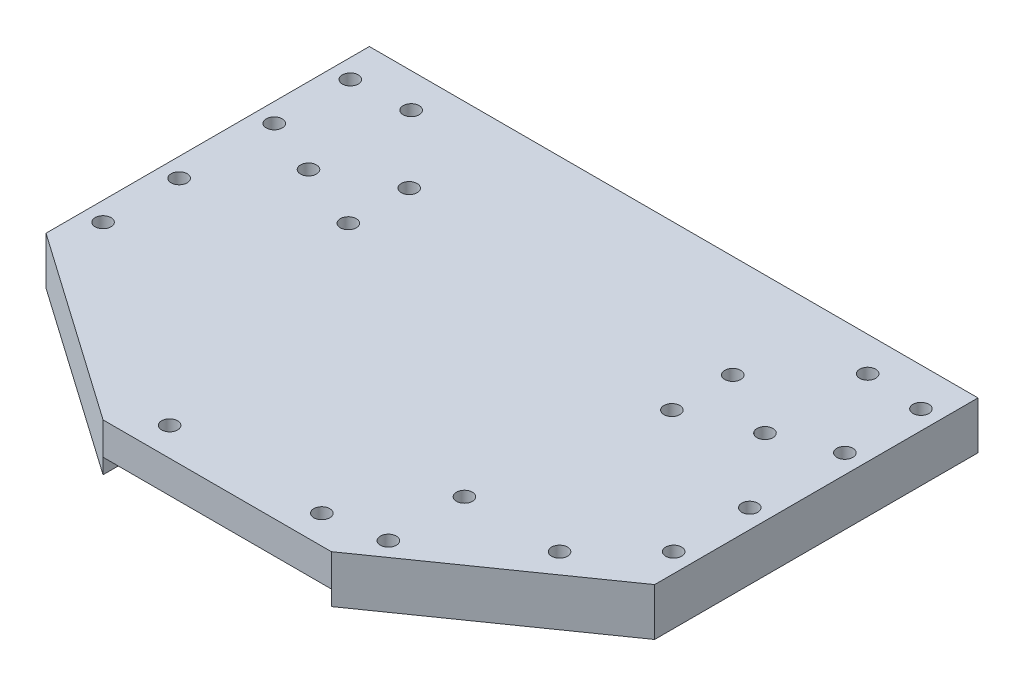
SolidWorks part; units mm, degrees
ref_plane "Front Plane" through (0, 0, 0) normal (0, 0, 1) x (1, 0, 0)
ref_plane "Top Plane" through (0, 0, 0) normal (0, 1, 0) x (1, 0, 0)
ref_plane "Right Plane" through (0, 0, 0) normal (1, 0, 0) x (0, 0, -1)
sketch "Sketch1" plane through (0, 0, 0) normal (0, 1, 0) x (1, 0, 0)
  line L2 (-80, -42.5) -> (-80, 42.5)
  line L3 (-80, 42.5) -> (80, 42.5)
  line L4 (80, -42.5) -> (80, 42.5)
  line L9 (-80, -42.5) -> (-30, -77.5)
  line L12 (-30, -77.5) -> (30, -77.5)
  line L14 (30, -77.5) -> (80, -42.5)
  point P0 (0, 0)
  dimension "D1" = 85
  dimension "D2" = 160
  dimension "D3" = 60
extrude "Boss-Extrude2" add sketch "Sketch1" along normal blind 12.5
sketch "Sketch2" plane through (0, 12.5, 0) normal (0, 1, 0) x (1, 0, 0)
  line L0 (0, 42.5) -> (0, 2.75) construction
  line L1 (80, 42.5) -> (-80, 42.5) construction
  line L2 (-30, -77.5) -> (30, -77.5) construction
  line L3 (-15, -27.25) -> (15, -27.25) construction
  line L4 (-10.25, -47.5) -> (10.25, -47.5)
  line L5 (-10.25, -47.5) -> (-10.25, -7)
  line L6 (-10.25, -7) -> (-3, -7)
  line L7 (10.25, -47.5) -> (10.25, -7)
  line L8 (-10.25, -47.5) -> (10.25, -7) construction
  line L9 (-10.25, -7) -> (10.25, -47.5) construction
  line L10 (-15, -57.25) -> (15, -57.25)
  line L11 (-15, -57.25) -> (-15, 2.75)
  line L12 (-15, 2.75) -> (15, 2.75)
  line L13 (15, -57.25) -> (15, 2.75)
  line L14 (-15, -57.25) -> (15, 2.75) construction
  line L15 (-15, 2.75) -> (15, -57.25) construction
  line L16 (3, -7) -> (3, 2.75)
  line L19 (3, 2.75) -> (-3, 2.75)
  line L20 (-3, -7) -> (-3, 2.75)
  line L21 (0, -7) -> (0, -77.5) construction
  line L22 (3, -7) -> (10.25, -7)
  circle A0 centre (-5, -51.5) radius 2.1
  circle A1 centre (5, -51.5) radius 2.1
  circle A2 centre (5, -3) radius 2.1
  circle A3 centre (-5, -3) radius 2.1
  point P6 (0, -27.25)
  point P11 (0, -27.25)
  dimension "D6" = 5
  dimension "D7" = 4
  dimension "D8" = 4.2
  dimension "D1" = 20.5
  dimension "D2" = 40.5
  dimension "D3" = 30
  dimension "D4" = 60
  dimension "D5" = 30
  dimension "D9" = 3
extrude "Boss-Extrude3" add sketch "Sketch2" along normal blind 29 contours L20 A3 L12 L11 L10 L13 L16 A2 L22 L7 L4 L5 L6 A0 A1
sketch "Sketch4" plane through (0, 0, 57.25) normal (0, 0, 1) x (1, 0, 0)
  line L0 (-5, 41.5) -> (-5, 12.5) construction
  line L1 (-15, 41.5) -> (15, 41.5) construction
  line L2 (-15, 12.5) -> (15, 12.5) construction
  line L3 (0, 41.5) -> (0, 12.5) construction
  line L4 (5, 41.5) -> (5, 12.5) construction
  line L5 (9.5, 37.5) -> (0.5, 37.5)
  line L6 (-9.5, 34) -> (-0.5, 34)
  line L7 (-9.5, 34) -> (-9.5, 37.5)
  line L8 (-9.5, 37.5) -> (-0.5, 37.5)
  line L9 (-0.5, 34) -> (-0.5, 37.5)
  line L10 (-9.5, 34) -> (-0.5, 37.5) construction
  line L11 (-9.5, 37.5) -> (-0.5, 34) construction
  line L12 (0.5, 34) -> (0.5, 37.5)
  line L13 (9.5, 34) -> (0.5, 34)
  line L14 (9.5, 34) -> (9.5, 37.5)
  point P10 (-5, 35.75)
  dimension "D1" = 5
  dimension "D2" = 9
  dimension "D3" = 3.5
  dimension "D4" = 4
extrude "Cut-Extrude1" cut sketch "Sketch4" against normal blind 73
chamfer "Chamfer1" distance 3 angle 45 4 edges at (-15, 27, -2.75) (15, 27, -2.75) (-15, 27, 57.25) (15, 27, 57.25)
sketch "Sketch5" plane through (0, 0, 0) normal (0, -1, 0) x (1, 0, 0)
  line L0 (-30, 70) -> (30, 70) construction
  line L1 (-30, 77.5) -> (30, 77.5)
  line L2 (-30, 77.5) -> (-30, 62.5)
  line L3 (-30, 62.5) -> (30, 62.5)
  line L4 (30, 77.5) -> (30, 62.5)
  line L5 (0, 77.5) -> (0, 62.5) construction
  circle A0 centre (-20, 70) radius 2.8976
  circle A1 centre (20, 70) radius 2.8976
  point P11 (0, 70)
  dimension "D2" = 20
  dimension "D1" = 15
extrude "Cut-Extrude2" cut sketch "Sketch5" against normal blind 4
sketch "Sketch6" plane through (0, 0, 0) normal (0, -1, 0) x (-1, 0, 0)
  circle A0 centre (20, -70) radius 2.8976
  circle A1 centre (-20, -70) radius 2.8976
extrude "Cut-Extrude3" cut sketch "Sketch6" against normal blind 26
sketch "Sketch7" plane through (0, 12.5, 0) normal (0, 1, 0) x (1, 0, 0)
  line L0 (-75, 34.6) -> (-75, 30.4) construction
  line L5 (-75, 14.6) -> (-75, 10.4) construction
  line L6 (0, 42.5) -> (0, -77.5) construction
  line L7 (80, 42.5) -> (-80, 42.5) construction
  line L8 (-30, -77.5) -> (30, -77.5) construction
  line L10 (75, 34.6) -> (75, 30.4) construction
  line L15 (-75, -10.4) -> (-75, -14.6) construction
  line L16 (-75, -30.4) -> (-75, -34.6) construction
  line L17 (75, -10.4) -> (75, -14.6) construction
  line L18 (75, -30.4) -> (75, -34.6) construction
  line L19 (75, 14.6) -> (75, 10.4) construction
  circle A0 centre (-75, 32.5) radius 2.1
  circle A1 centre (-75, 12.5) radius 2.1
  circle A2 centre (-75, -12.5) radius 2.1
  circle A3 centre (-75, -32.5) radius 2.1
  circle A4 centre (75, -32.5) radius 2.1
  circle A5 centre (75, -12.5) radius 2.1
  circle A6 centre (75, 12.5) radius 2.1
  circle A7 centre (75, 32.5) radius 2.1
  dimension "D2" = 4.2
  dimension "D4" = 4.2
extrude "Cut-Extrude4" cut sketch "Sketch7" against normal blind 26
sketch "Sketch8" plane through (0, 0, 0) normal (0, -1, 0) x (1, 0, 0)
  line L0 (0, 77.5) -> (0, -42.5) construction
  line L5 (30, 77.5) -> (-30, 77.5) construction
  line L6 (80, -42.5) -> (-80, -42.5) construction
  line L7 (-60, 2.5) -> (-60, -8.6) construction
  line L8 (-70, -42.5) -> (-60, -42.5)
  line L12 (-60, -20) -> (-70, -20) construction
  line L13 (-60, -31.4) -> (-60, -42.5) construction
  circle A0 centre (-60, -6.5) radius 2.1
  circle A1 centre (-60, -33.5) radius 2.1
  circle A2 centre (60, -33.5) radius 2.1
  circle A3 centre (60, -6.5) radius 2.1
  dimension "D4" = 4.2
extrude "Cut-Extrude5" cut sketch "Sketch8" against normal blind 26 contours A0 | A1 | A3 | A2
sketch "Sketch9" plane through (0, 0, 0) normal (0, -1, 0) x (1, 0, 0)
  line L0 (-60, -33.5) -> (-60, -6.5) construction
  line L1 (80, -42.5) -> (-80, -42.5) construction
  line L2 (-70, -42.5) -> (-50, -42.5)
  line L3 (-70, -42.5) -> (-70, 2.5)
  line L4 (-70, 2.5) -> (-50, 2.5)
  line L5 (-50, -42.5) -> (-50, 2.5)
  line L6 (-80, -42.5) -> (-80, 42.5) construction
  line L7 (0, 77.5) -> (0, -43.6165) construction
  line L8 (30, 77.5) -> (-30, 77.5) construction
  line L9 (70, 2.5) -> (50, 2.5)
  line L10 (50, -42.5) -> (50, 2.5)
  line L11 (70, -42.5) -> (50, -42.5)
  line L12 (70, -42.5) -> (70, 2.5)
  dimension "D1" = 10
  dimension "D2" = 20
  dimension "D3" = 45
extrude "Cut-Extrude8" cut sketch "Sketch9" against normal blind 5
sketch "Sketch10" plane through (0, 0, 57.25) normal (0, 0, 1) x (1, 0, 0)
  line L0 (-0.5, 35.75) -> (0.5, 35.75) construction
  line L1 (-0.5, 34) -> (-0.5, 37.5) construction
  line L2 (0.5, 37.5) -> (0.5, 34) construction
  line L3 (9.5, 37.5) -> (0.5, 37.5) construction
  line L4 (-0.75, 34) -> (0.75, 34)
  line L5 (-0.75, 34) -> (-0.75, 37.5)
  line L6 (-0.75, 37.5) -> (0.75, 37.5)
  line L7 (0.75, 34) -> (0.75, 37.5)
  line L8 (-0.75, 34) -> (0.75, 37.5) construction
  line L9 (-0.75, 37.5) -> (0.75, 34) construction
  point P6 (0, 35.75)
  dimension "D1" = 1.5
extrude "Boss-Extrude4" add sketch "Sketch10" against normal up to surface (9.75 mm away) up to face at (-5, 35.75, 47.5)
sketch "Sketch11" plane through (0, 12.5, 0) normal (0, 1, 0) x (1, 0, 0)
  line L0 (0, -77.5) -> (0, 42.5) construction
  line L1 (-30, -77.5) -> (30, -77.5) construction
  line L2 (80, 42.5) -> (-80, 42.5) construction
  line L3 (-12, 2.75) -> (-3, 2.75) construction
  line L4 (0, 17.75) -> (-47.61, 17.75)
  line L5 (0, 17.75) -> (0, 42.75)
  line L6 (0, 42.75) -> (-47.61, 42.75)
  line L7 (-47.61, 17.75) -> (-47.61, 42.75)
  line L8 (-32.5, 42.75) -> (-32.5, 17.75) construction
  line L9 (-47.61, 30.25) -> (0, 30.25) construction
  circle A0 centre (-42.5, 37.25) radius 2.1
  circle A1 centre (-42.5, 23.25) radius 2.1
  dimension "D5" = 4.2
  dimension "D6" = 7
  dimension "D7" = 10
  dimension "D1" = 47.61
  dimension "D2" = 25
  dimension "D3" = 15
  dimension "D4" = 32.5
extrude "Cut-Extrude9" cut sketch "Sketch11" against normal blind 22 contours A0 | A1
sketch "Sketch12" plane through (0, 12.5, 0) normal (0, 1, 0) x (1, 0, 0)
  circle A0 centre (-42.5, 37.25) radius 2.1
  circle A1 centre (-42.5, 23.25) radius 2.1
extrude "Boss-Extrude5" add sketch "Sketch12" against normal through all
sketch "Sketch13" plane through (0, 41.5, 0) normal (0, 1, 0) x (1, 0, 0)
  line L1 (-18.0115, -62.004) -> (18.0115, -62.004)
  line L2 (-18.0115, -62.004) -> (-18.0115, 7.9434)
  line L3 (-18.0115, 7.9434) -> (18.0115, 7.9434)
  line L4 (18.0115, -62.004) -> (18.0115, 7.9434)
  line L5 (-18.0115, -62.004) -> (18.0115, 7.9434) construction
  line L6 (-18.0115, 7.9434) -> (18.0115, -62.004) construction
  point P0 (0, -27.0303)
extrude "Cut-Extrude10" cut sketch "Sketch13" against normal up to surface (29 mm away) up to face at (-5, 12.5, 53.6)
sketch "Sketch14" plane through (0, 12.5, 0) normal (0, 1, 0) x (1, 0, 0)
  circle A0 centre (-20, -70) radius 2.1
  circle A1 centre (20, -70) radius 2.1
  circle A2 centre (-20, -70) radius 2.8976
  circle A3 centre (20, -70) radius 2.8976
  dimension "D1" = 4.2
  dimension "D2" = 4.2
extrude "Boss-Extrude6" add sketch "Sketch14" against normal up to surface (8.5 mm away) up to face at (20, 4, 67.1024)
sketch "Sketch15" plane through (0, 12.5, 0) normal (0, 1, 0) x (1, 0, 0)
  line L0 (0, 42.5) -> (0, -77.5) construction
  line L1 (80, 42.5) -> (-80, 42.5) construction
  line L2 (-30, -77.5) -> (30, -77.5) construction
  line L3 (-47.53, 7.5) -> (0, 7.5) construction
  line L4 (0, 42.5) -> (-47.53, 42.5)
  line L5 (0, 42.5) -> (0, 22.5)
  line L6 (0, 22.5) -> (-47.53, 22.5)
  line L7 (-47.53, 42.5) -> (-47.53, 22.5)
  line L8 (0, 22.5) -> (-47.53, 22.5)
  line L9 (0, 22.5) -> (0, -7.5)
  line L10 (0, -7.5) -> (-47.53, -7.5)
  line L11 (-47.53, 22.5) -> (-47.53, -7.5)
  circle A0 centre (-42.53, 15.5) radius 2.1
  circle A1 centre (-42.53, -0.5) radius 2.1
  circle A2 centre (42.53, -0.5) radius 2.1
  circle A3 centre (42.53, 15.5) radius 2.1
  dimension "D4" = 4.2
  dimension "D5" = 16
  dimension "D6" = 4.2
  dimension "D7" = 5
  dimension "D8" = 5
  dimension "D9" = 8
  dimension "D1" = 47.53
  dimension "D2" = 20
  dimension "D3" = 30
extrude "Cut-Extrude11" cut sketch "Sketch15" against normal blind 38 contours A0 | A1 | A3 | A2
sketch "Sketch16" plane through (0, 12.5, 0) normal (0, 1, 0) x (1, 0, 0)
  line L0 (30, -77.5) -> (80, -42.5)
  line L2 (30, -77.5) -> (30, -42.5)
  line L3 (30, -42.5) -> (80, -42.5)
  circle A0 centre (35, -47.5) radius 2.1
  circle A1 centre (35, -67.5) radius 2.1
  circle A2 centre (60, -47.5) radius 2.1
  dimension "D1" = 4.2
  dimension "D2" = 4.2
  dimension "D3" = 4.2
  dimension "D4" = 5
  dimension "D5" = 5
  dimension "D6" = 30
  dimension "D7" = 5
  dimension "D8" = 25
  dimension "D9" = 5
extrude "Cut-Extrude12" cut sketch "Sketch16" against normal blind 38 contours A0 | A2 | A1
